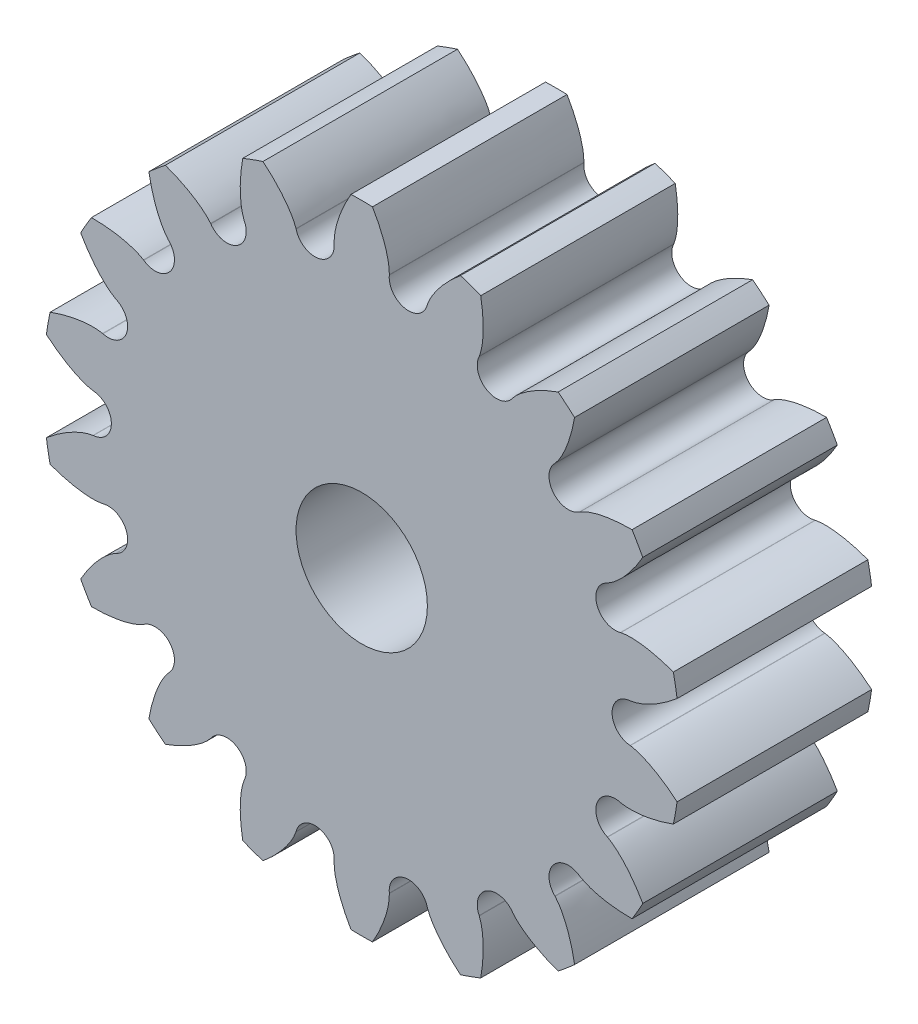
SolidWorks part; units mm, degrees
material "PE Low/Medium Density"
ref_plane "Front Plane" through (0, 0, 0) normal (0, 0, 1) x (1, 0, 0)
ref_plane "Top Plane" through (0, 0, 0) normal (0, 1, 0) x (1, 0, 0)
ref_plane "Right Plane" through (0, 0, 0) normal (1, 0, 0) x (0, 0, -1)
sketch "Involute construction sketch" plane through (0, 0, 0) normal (0, 0, 1) x (1, 0, 0)
  line L0 (0, 0) -> (-1.8, 3.7586) construction
  line L1 (0, 0) -> (-1.0856, 4.0235) construction
  line L2 (0, 0) -> (-0.3348, 4.1539) construction
  line L3 (0, 0) -> (0.4271, 4.1454) construction
  line L4 (-3.0265, 2.8648) -> (-2.4543, 3.368) construction
  line L5 (-2.4543, 3.368) -> (-1.8, 3.7586) construction
  line L6 (-1.8, 3.7586) -> (-1.0856, 4.0235) construction
  line L7 (0, 0) -> (-2.4543, 3.368) construction
  line L8 (0, 0) -> (-3.0265, 2.8648) construction
  line L9 (-1.0856, 4.0235) -> (-0.3348, 4.1539) construction
  line L10 (-0.3348, 4.1539) -> (0.4271, 4.1454) construction
  line L11 (-3.0265, 2.8648) -> (-0.4074, 5.6318) construction
  line L12 (-2.4543, 3.368) -> (0.009, 5.1631) construction
  line L13 (-1.8, 3.7586) -> (0.2617, 4.746) construction
  line L14 (-1.0856, 4.0235) -> (0.3858, 4.4205) construction
  line L15 (-0.3348, 4.1539) -> (0.4247, 4.2151) construction
  line L17 (0, 0) -> (0, 5.7859) construction
  line L18 (0, 0) -> (0.3865, 4.418) construction
  line L19 (0, 0) -> (0.6726, 3.8147) construction
  circle A0 centre (0, 0) radius 3.8735 construction
  circle A1 centre (0, 0) radius 4.1674 construction
  circle A2 centre (0, 0) radius 4.4348 construction
  circle A3 centre (0, 0) radius 4.9276 construction
  spline S0 degree 3 poles (0.4271, 4.1454) (0.4284, 4.2386) (0.3887, 4.4458) (0.1758, 4.9887) (-0.14, 5.3768) (-0.4074, 5.6318) knots 0 0 0 0 0.160044 0.360037 1 1 1 1 construction
  point P17 (0.1663, 4.9248)
  dimension "D1" = 7.747
  dimension "D2" = 8.3348
  dimension "D3" = 8.8697
  dimension "D4" = 9.8552
  dimension "D5" = 0.762
  dimension "D6" = 1.524
  dimension "D7" = 2.286
  dimension "D8" = 3.048
  dimension "D9" = 3.81
  dimension "D10" = 5
  dimension "D11" = 10
sketch "Sketch2" plane through (0, 0, 0) normal (0, 0, 1) x (1, 0, 0)
  line L0 (0, 4.9276) -> (0, 3.8735)
  line L1 (0, 0) -> (0, 5.7859) construction
  line L2 (0.4271, 4.1454) -> (0.4266, 4.1404)
  line L3 (0, 0) -> (0.4271, 4.1454) construction
  circle A0 centre (0, 0) radius 4.9276 construction
  circle A1 centre (0, 0) radius 3.8735 construction
  arc A2 (0, 4.9276) -> (0.1663, 4.9248) centre (0, 0) cw
  arc A3 (0, 3.8735) -> (0.6726, 3.8147) centre (0, 0) cw
  arc A4 (0.4266, 4.1404) -> (0.6726, 3.8147) centre (0.7247, 4.1097) ccw
  spline S0 degree 3 poles (0.1663, 4.9248) (0.2589, 4.7664) (0.3758, 4.5128) (0.4284, 4.2386) (0.4271, 4.1454) knots 0 0 0 0 0.664052 1 1 1 1
sketch "Sketch3" plane through (0, 0, 0) normal (0, 0, 1) x (1, 0, 0)
  circle A0 centre (0, 0) radius 3.8735
  circle A1 centre (0, 0) radius 1.016
  dimension "D1" = 7.747
  dimension "D2" = 2.032
extrude "Base" add sketch "Sketch3" along normal blind 3.0099
extrude "Half tooth" add sketch "Sketch2" along normal up to surface (3.0099 mm away) up to face at (3.8735, 0, 3.0099)
ref_plane "Midplane of half tooth" through (0, 0, 0) normal (-1, 0, 0) x (0, 0, 1)
mirror "Mirror of half tooth" about plane through (0, 0, 0) normal (-1, 0, 0) of "Half tooth"
pattern_circular "Pattern of tooth" count 18 over 360 about axis through (0, 0, 3.0099) along (0, 0, 1) of "Half tooth", "Mirror of half tooth"
equation "\"radtodeg\"= 180 / PI'radian to degree conversion [ ]"
equation "\"phi\"= 20'pressure angle [deg]"
equation "\"N\"= 18'number of teeth [teeth]"
equation "\"A\"= 0.388in'diameter of addendum circle [inch]"
equation "\"B\"= 0.305in'diameter of dedendum circle [inch]"
equation "\"P\"= ( \"N\" + 2 ) / \"A\"'diametral pitch [teeth/inch]"
equation "\"d\"= \"N\" / \"P\"'diameter of pitch circle [inch]"
equation "\"cp\"= PI / \"P\"'circular pitch [inch/teeth]"
equation "\"add\"= 1 / \"P\"'addendum [inch]"
equation "\"ded\"= - ( \"B\" - \"d\" ) / 2'dedendum [inch]"
equation "\"clear\"= \"ded\" - \"add\"'clearance [inch]"
equation "\"C\"= \"B\" + 2 * \"clear\"'diameter of clearance circle [inch]"
equation "\"h\"= \"add\" + \"ded\"'tooth height / whole depth [inch]"
equation "\"s\"= \"d\" * cos ( \"phi\" * 1 / \"radtodeg\" )'diameter of base circle [inch]"
equation "\"t\"= ( PI / 2 ) / \"P\"'tooth width at diameter of pitch circle diameter [inch]"
equation "\"alpha\"= ( \"t\" / ( \"d\" / 2 ) * \"radtodeg\" ) / 2'arc angle for half of tooth width at pitch circle diameter [inch]"
equation "\"bore\"= 0.0800'bore of hub [inch]"
equation "\"D4@Involute construction sketch\"= \"A\"'addendum circle"
equation "\"D3@Involute construction sketch\"= \"d\"'pitch circle"
equation "\"D2@Involute construction sketch\"= \"s\"'base circle"
equation "\"D1@Involute construction sketch\"= \"B\"'dedendum circle"
equation "\"seg\"= \"D5@Involute construction sketch\"'size of one involute segment [inch]"
equation "\"D6@Involute construction sketch\"=2*\"seg\""
equation "\"D7@Involute construction sketch\"=3*\"seg\""
equation "\"D8@Involute construction sketch\"=4*\"seg\""
equation "\"D9@Involute construction sketch\"=5*\"seg\""
equation "\"D10@Involute construction sketch\"=\"alpha\""
equation "\"D11@Involute construction sketch\"=2*\"alpha\""
equation "\"D1@Sketch3\"=\"B\""
equation "\"D1@CirPattern1\"=\"N\""
equation "\"D2@Sketch3\"=\"bore\""
